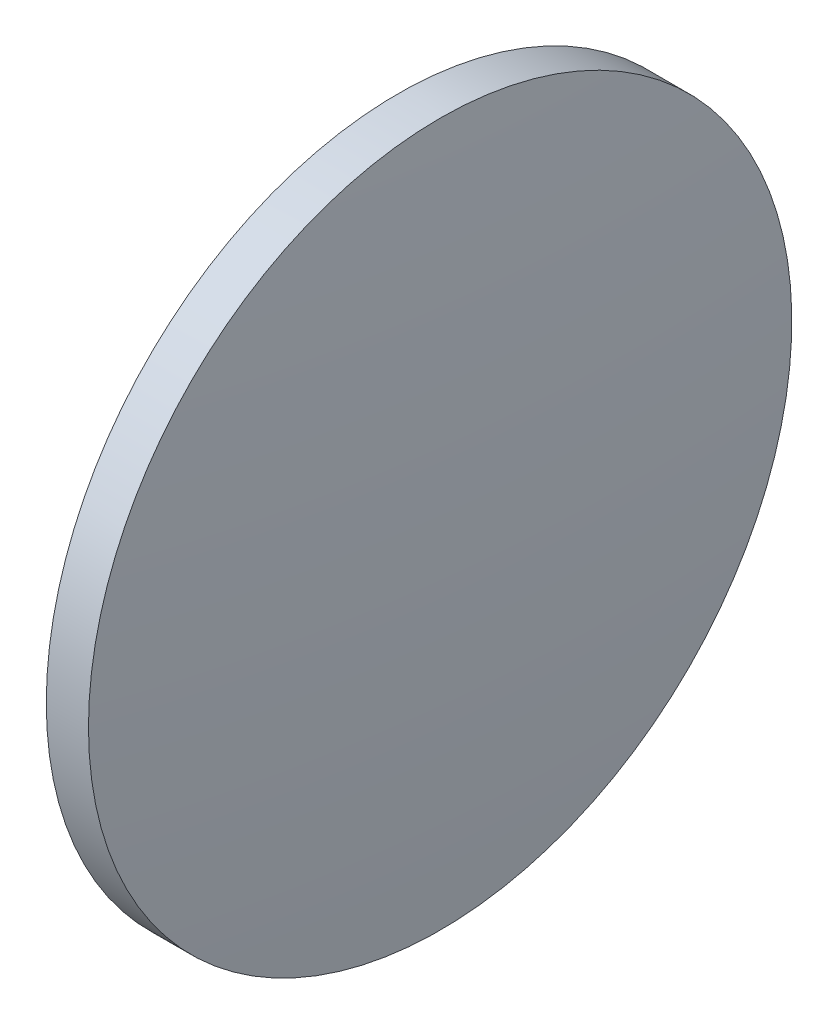
SolidWorks part; units mm, degrees
ref_plane "前视基准面" through (0, 0, 0) normal (0, 0, 1) x (1, 0, 0)
ref_plane "上视基准面" through (0, 0, 0) normal (0, 1, 0) x (1, 0, 0)
ref_plane "右视基准面" through (0, 0, 0) normal (1, 0, 0) x (0, 0, -1)
sketch "草图1" plane through (0, 0, 0) normal (0, 0, 1) x (1, 0, 0)
  line L0 (490.6137, 143.8585) -> (500.2017, 143.8585) construction
  line L1 (492.9793, 143.8585) -> (492.9793, 156.3585)
  line L2 (494.9793, 143.8585) -> (492.9793, 143.8585)
  line L5 (492.9793, 156.3585) -> (494.4793, 156.3585)
  arc A0 (494.9793, 143.8585) -> (494.4793, 156.3585) centre (338.4793, 143.8585) ccw
revolve "旋转1" add sketch "草图1" angle 360 about L0
